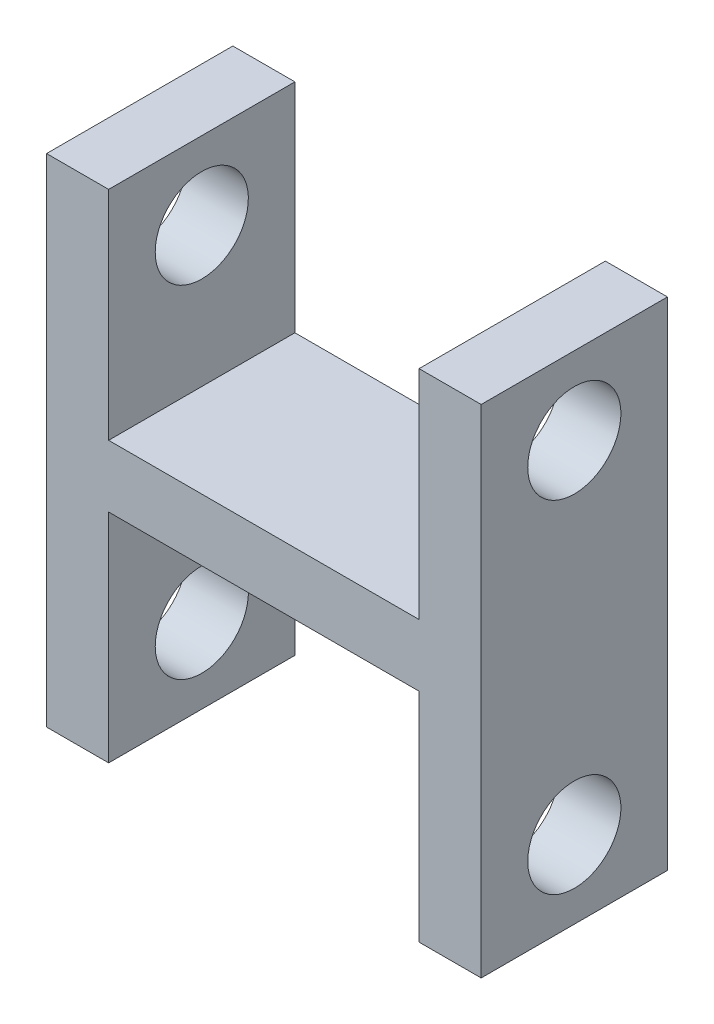
SolidWorks part; units mm, degrees
ref_plane "Front Plane" through (0, 0, 0) normal (0, 0, 1) x (1, 0, 0)
ref_plane "Top Plane" through (0, 0, 0) normal (0, 1, 0) x (1, 0, 0)
ref_plane "Right Plane" through (0, 0, 0) normal (1, 0, 0) x (0, 0, -1)
sketch "Sketch1" plane through (0, 0, 0) normal (0, 0, 1) x (1, 0, 0)
  line L1 (0, 0) -> (177.8, 0)
  line L2 (0, 0) -> (0, 203.2)
  line L3 (0, 203.2) -> (177.8, 203.2)
  line L4 (177.8, 0) -> (177.8, 203.2)
  dimension "D1" = 177.8
  dimension "D2" = 203.2
extrude "Boss-Extrude2" add sketch "Sketch1" along normal blind 76.2
sketch "Sketch3" plane through (0, 0, 76.2) normal (0, 0, 1) x (1, 0, 0)
  line L0 (177.8, 203.2) -> (0, 203.2) construction
  line L1 (25.4, 203.2) -> (152.4, 203.2)
  line L2 (25.4, 203.2) -> (25.4, 114.3)
  line L3 (25.4, 114.3) -> (152.4, 114.3)
  line L4 (152.4, 203.2) -> (152.4, 114.3)
  line L5 (0, 0) -> (177.8, 0) construction
  line L6 (25.4, 0) -> (152.4, 0)
  line L7 (25.4, 0) -> (25.4, 88.9)
  line L8 (25.4, 88.9) -> (152.4, 88.9)
  line L9 (152.4, 0) -> (152.4, 88.9)
  line L10 (0, 203.2) -> (0, 0) construction
  line L11 (177.8, 0) -> (177.8, 203.2) construction
  dimension "D1" = 25.4
  dimension "D2" = 25.4
  dimension "D3" = 25.4
  dimension "D4" = 25.4
  dimension "D5" = 25.4
  dimension "D6" = 88.9
extrude "Cut-Extrude1" cut sketch "Sketch3" against normal blind 76.2
sketch "Sketch4" plane through (0, 0, 0) normal (-1, 0, 0) x (0, 0, 1)
  line L0 (76.2, 203.2) -> (0, 203.2) construction
  line L1 (76.2, 0) -> (0, 0) construction
  line L2 (76.2, 203.2) -> (76.2, 0) construction
  circle A0 centre (38.1, 171.45) radius 19.05
  circle A1 centre (38.1, 31.75) radius 19.05
  point P4 (38.1, 203.2)
  dimension "D1" = 38.1
  dimension "D2" = 38.1
  dimension "D5" = 38.1
  dimension "D3" = 31.75
  dimension "D4" = 31.75
  dimension "D6" = 38.1
extrude "Cut-Extrude3" cut sketch "Sketch4" against normal blind 199.898
